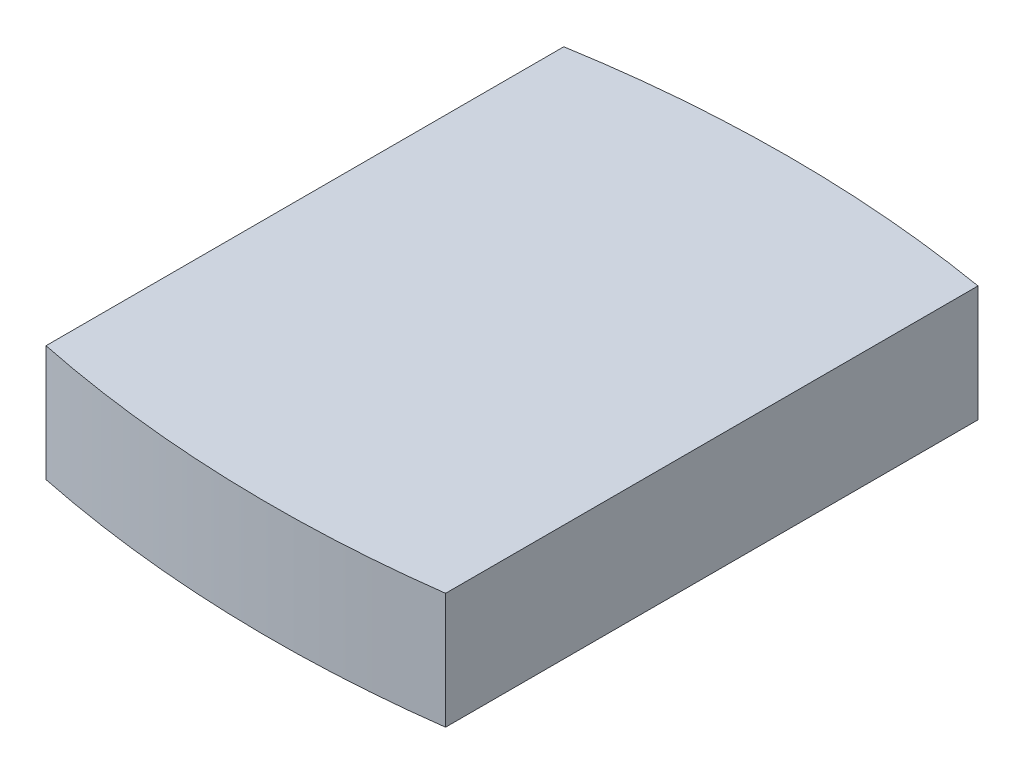
SolidWorks part; units mm, degrees
ref_plane "Спереди" through (0, 0, 0) normal (0, 0, 1) x (1, 0, 0)
ref_plane "Сверху" through (0, 0, 0) normal (0, 1, 0) x (1, 0, 0)
ref_plane "Справа" through (0, 0, 0) normal (1, 0, 0) x (0, 0, -1)
sketch "Эскиз1" plane through (0, 0, 0) normal (0, 1, 0) x (1, 0, 0)
  line L0 (0, 0) -> (0, 25)
  line L1 (20, 25) -> (20, -0.707)
  arc A0 (0, 25) -> (20, 25) centre (10, -34.1608) cw
  arc A1 (0, 0) -> (20, -0.707) centre (12.09, 58.7693) ccw
extrude "Бобышка-Вытянуть1" add sketch "Эскиз1" along normal blind 5.6
